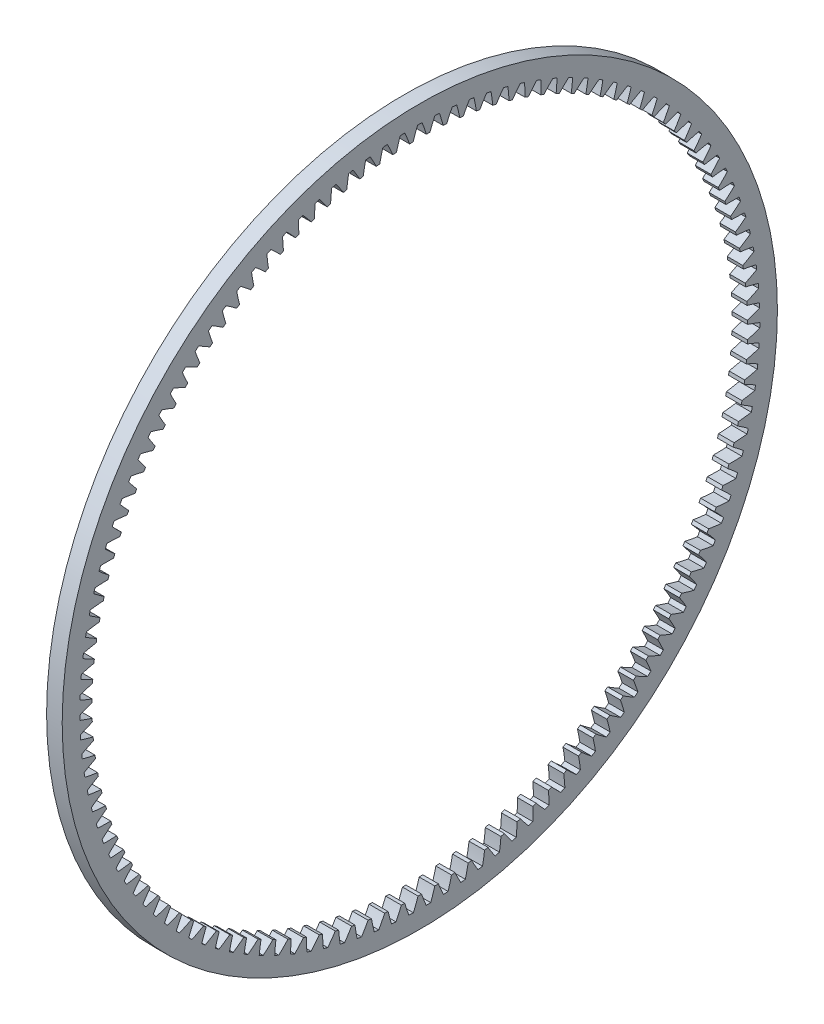
SolidWorks part; units mm, degrees
ref_plane "Plane1" through (0, 0, 0) normal (0, 0, 1) x (1, 0, 0)
ref_plane "Plane2" through (0, 0, 0) normal (0, 1, 0) x (1, 0, 0)
ref_plane "Plane3" through (0, 0, 0) normal (1, 0, 0) x (0, 0, -1)
sketch "HoldingSke" plane through (0, 0, 0) normal (0, 1, 0) x (1, 0, 0)
  line L0 (0, 0) -> (-332.012, -511.2536)
  line L1 (-15, 0) -> (100, 0) construction
  line L2 (0, 0) -> (-2.1039, 2.3779)
  line L3 (0, 0) -> (-11.863, 4.5341)
  line L4 (0, 0) -> (-4.7035, 7.2428)
  line L5 (0, 0) -> (-23.7986, -8.8762)
  line L6 (0, 0) -> (-10.5278, -7.1032)
  line L7 (-2.1039, 2.3779) -> (3.3635, 27.1825)
  line L8 (-76.2, 54.61) -> (-54.61, 54.61)
  line L9 (-71.009, 38.7566) -> (-53.1078, 45.2721)
  line L10 (-76.2, 71.12) -> (104.1128, 71.12)
  line L11 (0, 0) -> (-3.048, 0)
  line L12 (-76.2, 101.6) -> (-76.1573, 101.6)
  line L13 (24.9733, 27.94) -> (52.9518, 28.4284)
  line L14 (24.9733, 27.94) -> (25.0241, 27.9398)
  line L15 (24.9733, 27.94) -> (100.4021, 29.52)
  circle A0 centre (0, 0) radius 69.85
  circle A1 centre (0, 0) radius 12.7
  circle A2 centre (0, 0) radius 12.7
  dimension "MHD" = 25.4
  dimension "Hub_dia" = 25.4
  dimension "Diameter" = 139.7
  dimension "Num_teeth" = 123
  dimension "Pitch_radius" = 180.3128
  dimension "Pitch" = 609.6
  dimension "Width" = 3.048
  dimension "Overall_len" = 25.4
  dimension "Show_teeth" = 123
  dimension "Thickness" = 12.7
  dimension "OAL" = 25.4001
  dimension "T_dim" = 21.59
  dimension "Ap" = 20
  dimension "H" = 19.05
  dimension "Backlash" = 0.0427
  dimension "Addendum_fac" = 1
  dimension "Dedendum_fac" = 1.2
  dimension "Clearance_fac" = 0.2
  dimension "Dedendum_add" = 0.0508
sketch "BasProSke" plane through (0, 0, 0) normal (0, 1, 0) x (1, 0, 0)
  line L0 (-10, 0) -> (60, 0) construction
  line L1 (0, 64.0292) -> (0, 69.85)
  line L2 (0, 64.0292) -> (3.048, 64.0292)
  line L3 (3.048, 64.0292) -> (3.048, 69.85)
  line L4 (3.048, 69.85) -> (0, 69.85)
  dimension "Diameter" = 139.7
  dimension "Thickness" = 3.048
  dimension "Inside_diameter" = 128.0583
revolve "Base-Revolve" add sketch "BasProSke" angle 360 about L0
sketch "TooCutSke" plane through (0, 0, 0) normal (1, 0, 0) x (0, 0, -1)
  line L3 (0.9379, 65.0807) -> (0.9379, 53.6633) construction
  line L4 (0, 0) -> (0, 59.563) construction
  line L5 (0, 0) -> (-1.745, 68.3052) construction
  line L6 (-29.7696, 54.3035) -> (36.4247, 55.9945) construction
  circle A0 centre (0, 0) radius 65.0875 construction
  circle A1 centre (0, 0) radius 66.4083 construction
  circle A2 centre (0, 0) radius 55.046 construction
  circle A3 centre (0, 0) radius 64.0038 construction
  arc A4 (1.299, 63.9906) -> (0.4398, 66.4068) centre (-29.7696, 54.3035) ccw
  arc A5 (1.299, 63.9906) -> (-1.299, 63.9906) centre (0, 0) ccw
  arc A6 (0.4398, 66.4068) -> (-0.4398, 66.4068) centre (0, 0) ccw
  arc A7 (-0.4398, 66.4068) -> (-1.299, 63.9906) centre (29.7696, 54.3035) ccw
  dimension "Pitch_dia" = 130.175
  dimension "Base_dia" = 110.092
  dimension "Root_dia" = 132.8166
  dimension "Overcut_dia" = 128.0075
  dimension "Flank_rad" = 32.5437
  dimension "Half_ang" = 1.463
  dimension "Half_CT" = 0.9379
extrude "ToothCut" cut sketch "TooCutSke" along normal through all
fillet "Breaks" [suppressed] radius 0.1058
fillet "RootFillets" [suppressed] radius 0.2625
pattern_circular "TeethCuts" count 123 every 2.927 about axis through (-10, 0, 0) along (1, 0, 0) of "ToothCut"
equation "' \"Pitch@HoldingSke\" = 4"
equation "' \"Num_teeth@HoldingSke\" = 24"
equation "' \"Ap@HoldingSke\" =  14.5"
equation "' \"Width@HoldingSke\" = 0.5"
equation "' \"Diameter@HoldingSke\" = 8"
equation "' \"Show_teeth@HoldingSke\" = 100"
equation "' \"Backlash@HoldingSke\" = 0.009"
equation "' \"Addendum_fac@HoldingSke\" = 1.0"
equation "' \"Dedendum_fac@HoldingSke\" = 1.25"
equation "' \"Dedendum_add@HoldingSke\" = 0.00005"
equation "' \"Clearance_fac@HoldingSke\" = 0.25"
equation "\"Overcut_dia@TooCutSke\" = (\"Num_teeth@HoldingSke\" - 2 * \"Addendum_fac@HoldingSke\") / \"Pitch@HoldingSke\" - 0.002"
equation "\"Pitch_dia@TooCutSke\" = \"Num_teeth@HoldingSke\" / \"Pitch@HoldingSke\""
equation "\"Base_dia@TooCutSke\" = \"Num_teeth@HoldingSke\" / \"Pitch@HoldingSke\" * cos((\"Ap@HoldingSke\"  * 3.14159265 / 180)) * 0.90"
equation "\"Root_dia@TooCutSke\" = \"Num_teeth@HoldingSke\"  / \"Pitch@HoldingSke\" + 2 *  \"Dedendum_fac@HoldingSke\"/ \"Pitch@HoldingSke\" + \"Dedendum_add@HoldingSke\" * 2"
equation "\"Half_ang@TooCutSke\" = 180 / \"Num_teeth@HoldingSke\""
equation "\"Half_CT@TooCutSke\" = \"Num_teeth@HoldingSke\" / \"Pitch@HoldingSke\" * sin((3.14159265 / 2 / \"Num_teeth@HoldingSke\")) / 2 + 10 * \"Backlash@HoldingSke\" / 4"
equation "\"Flank_rad@TooCutSke\" = \"Num_teeth@HoldingSke\" / \"Pitch@HoldingSke\" / 4"
equation "\"Radius@RootFillets\"= \"Clearance_fac@HoldingSke\" / \"Pitch@HoldingSke\" + \"Dedendum_add@HoldingSke\""
equation "\"Break_rad@Breaks\" = 0.02 / \"Pitch@HoldingSke\" * 5"
equation "\"Num_teeth@TeethCuts\" = int( \"Show_teeth@HoldingSke\" ) + 1"
equation "\"Num_teeth@TeethCuts\" = ((sgn( \"Num_teeth@TeethCuts\" - \"Num_teeth@HoldingSke\" )-1)*( \"Num_teeth@TeethCuts\" - \"Num_teeth@HoldingSke\" ))/-2+ \"Num_teeth@HoldingSke\""
equation "\"Num_teeth@TeethCuts\" = ((sgn( \"Num_teeth@TeethCuts\" - 2.0)+1)*( \"Num_teeth@TeethCuts\" - 2.0))/2 +2.0"
equation "\"Angle@TeethCuts\" = 360.0 / \"Num_teeth@HoldingSke\""
equation "\"Diameter@BasProSke\" = \"Num_teeth@HoldingSke\"  / \"Pitch@HoldingSke\" + 2 *  \"Dedendum_fac@HoldingSke\"/ \"Pitch@HoldingSke\" + \"Dedendum_add@HoldingSke\" * 2 + 0.002"
equation "\"Diameter@BasProSke\" = ((sgn( \"Diameter@BasProSke\"  - \"Diameter@HoldingSke\" )+1)*( \"Diameter@BasProSke\"  - \"Diameter@HoldingSke\" ))/2 + \"Diameter@HoldingSke\""
equation "\"Inside_diameter@BasProSke\" =  (\"Num_teeth@HoldingSke\" - 2 * \"Addendum_fac@HoldingSke\") / \"Pitch@HoldingSke\" "
equation "\"Thickness@BasProSke\"  = \"Width@HoldingSke\""
